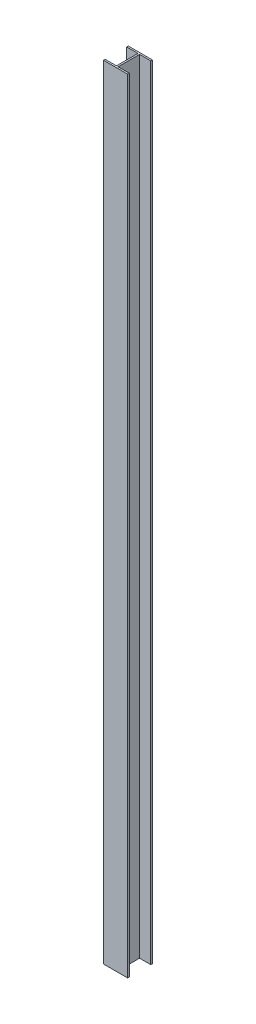
SolidWorks part; units mm, degrees
material "AISI 1010 Steel, hot rolled bar"
ref_plane "Front Plane" through (0, 0, 0) normal (0, 0, 1) x (1, 0, 0)
ref_plane "Top Plane" through (0, 0, 0) normal (0, 1, 0) x (1, 0, 0)
ref_plane "Right Plane" through (0, 0, 0) normal (1, 0, 0) x (0, 0, -1)
sketch "Sketch1" plane through (0, 0, 0) normal (0, 1, 0) x (1, 0, 0)
  line L12 (-51.5, 70.862) -> (51.5, 70.862)
  line L13 (51.5, 70.862) -> (51.5, 63.762)
  line L14 (51.5, 63.762) -> (3.55, 63.762)
  line L15 (3.55, 63.762) -> (3.55, -28.038)
  line L16 (3.55, -28.038) -> (51.5, -28.038)
  line L17 (51.5, -28.038) -> (51.5, -35.138)
  line L18 (51.5, -35.138) -> (-51.5, -35.138)
  line L19 (0, 70.862) -> (0, -49.2154) construction
  line L20 (-3.55, 63.762) -> (-3.55, -28.038)
  line L21 (-51.5, -28.038) -> (-51.5, -35.138)
  line L22 (-3.55, -28.038) -> (-51.5, -28.038)
  line L23 (-51.5, 63.762) -> (-3.55, 63.762)
  line L24 (-51.5, 70.862) -> (-51.5, 63.762)
  point P12 (0, -35.138)
  dimension "D1" = 7.1
  dimension "D2" = 91.8
  dimension "D3" = 106
  dimension "D4" = 103
  dimension "D5" = 55.05
  dimension "D6" = 47.95
extrude "Boss-Extrude1" add sketch "Sketch1" along normal blind 3352.8
sketch3d "3DSketch1"
  line L5 (-51.5, 0, 35.138) -> (51.5, 0, 35.138)
  line L6 (51.5, 0, 35.138) -> (51.5, 3352.8, 35.138)
  line L7 (51.5, 3352.8, 35.138) -> (-51.5, 3352.8, 35.138)
  line L8 (-51.5, 3352.8, 35.138) -> (-51.5, 0, 35.138)
  line L9 (-51.5, 0, 35.138) -> (51.5, 0, 35.138)
  line L10 (51.5, 0, 35.138) -> (51.5, 3352.8, 35.138)
  line L11 (51.5, 3352.8, 35.138) -> (-51.5, 3352.8, 35.138)
  line L12 (-51.5, 3352.8, 35.138) -> (-51.5, 0, 35.138)
  line L21 (51.5, 3352.8, -63.762) -> (51.5, 3352.8, -70.862)
  line L22 (51.5, 3352.8, -70.862) -> (-51.5, 3352.8, -70.862)
  line L23 (-51.5, 3352.8, -70.862) -> (-51.5, 3352.8, -63.762)
  line L24 (-51.5, 3352.8, -63.762) -> (-3.55, 3352.8, -63.762)
  line L25 (-3.55, 3352.8, -63.762) -> (-3.55, 3352.8, 28.038)
  line L26 (-3.55, 3352.8, 28.038) -> (-51.5, 3352.8, 28.038)
  line L27 (-51.5, 3352.8, 28.038) -> (-51.5, 3352.8, 35.138)
  line L28 (-51.5, 3352.8, 35.138) -> (51.5, 3352.8, 35.138)
  line L29 (51.5, 3352.8, 35.138) -> (51.5, 3352.8, 28.038)
  line L30 (51.5, 3352.8, 28.038) -> (3.55, 3352.8, 28.038)
  line L31 (3.55, 3352.8, 28.038) -> (3.55, 3352.8, -63.762)
  line L32 (3.55, 3352.8, -63.762) -> (51.5, 3352.8, -63.762)
  line L33 (51.5, 3352.8, -63.762) -> (51.5, 3352.8, -70.862)
  line L34 (51.5, 3352.8, -70.862) -> (-51.5, 3352.8, -70.862)
  line L35 (-51.5, 3352.8, -70.862) -> (-51.5, 3352.8, -63.762)
  line L36 (-51.5, 3352.8, -63.762) -> (-3.55, 3352.8, -63.762)
  line L37 (-3.55, 3352.8, -63.762) -> (-3.55, 3352.8, 28.038)
  line L38 (-3.55, 3352.8, 28.038) -> (-51.5, 3352.8, 28.038)
  line L39 (-51.5, 3352.8, 28.038) -> (-51.5, 3352.8, 35.138)
  line L40 (-51.5, 3352.8, 35.138) -> (51.5, 3352.8, 35.138)
  line L41 (51.5, 3352.8, 35.138) -> (51.5, 3352.8, 28.038)
  line L42 (51.5, 3352.8, 28.038) -> (3.55, 3352.8, 28.038)
  line L43 (3.55, 3352.8, 28.038) -> (3.55, 3352.8, -63.762)
  line L44 (3.55, 3352.8, -63.762) -> (51.5, 3352.8, -63.762)
  dimension "D1" = 0
  dimension "D3" = 103
  dimension "D4" = 3352.8
  dimension "D5" = 106
  dimension "D2" = 0
